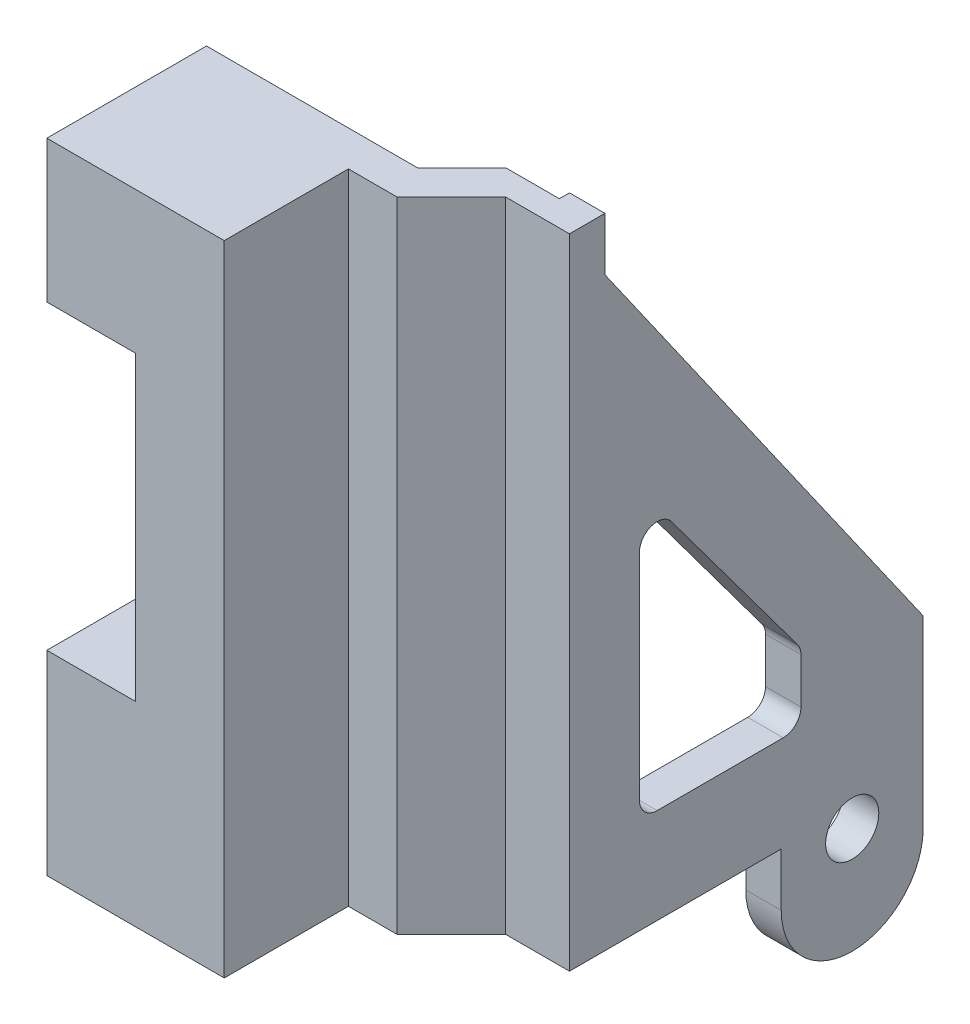
SolidWorks part; units mm, degrees
ref_plane "Front Plane" through (0, 0, 0) normal (0, 0, 1) x (1, 0, 0)
ref_plane "Top Plane" through (0, 0, 0) normal (0, 1, 0) x (1, 0, 0)
ref_plane "Right Plane" through (0, 0, 0) normal (1, 0, 0) x (0, 0, -1)
sketch "Sketch1" plane through (0, 0, 0) normal (0, 1, 0) x (1, 0, 0)
  line L0 (0, 0) -> (11.9097, 0)
  line L1 (11.9097, 0) -> (14.3993, 2.4897)
  line L2 (14.3993, 2.4897) -> (17.3993, 2.4897)
  line L3 (17.3993, 2.4897) -> (17.3993, 21)
  line L4 (0, 0) -> (0, -9)
  line L5 (0, -9) -> (10, -9)
  line L6 (10, -9) -> (10, -2)
  line L7 (10, -2) -> (12.7381, -2)
  line L8 (12.7381, -2) -> (15.7993, 1.0612)
  line L9 (15.7993, 1.0612) -> (19.3993, 1.0612)
  line L10 (19.3993, 1.0612) -> (19.3993, 21)
  line L11 (19.3993, 21) -> (17.3993, 21)
  dimension "D1" = 10
  dimension "D2" = 2.7381
  dimension "D3" = 4.3292
  dimension "D4" = 3
  dimension "D5" = 3.6
  dimension "D6" = 2
  dimension "D7" = 2
  dimension "D8" = 2
  dimension "D9" = 9
  dimension "D10" = 30
  dimension "D11" = 135
extrude "Boss-Extrude1" add sketch "Sketch1" along normal blind 36
sketch "Sketch2" plane through (19.3993, 0, 0) normal (1, 0, 0) x (0, 0, -1)
  line L0 (3.0612, 36) -> (3.0612, 33)
  line L1 (1.0612, 36) -> (21, 36) construction
  line L2 (3.0612, 33) -> (21, 7.3808)
  line L3 (21, 36) -> (21, 0) construction
  line L4 (21, 36) -> (21, 7.3808)
  line L5 (3.0612, 36) -> (21, 36)
  line L6 (1.0612, 36) -> (1.0612, 0) construction
  dimension "D1" = 2
  dimension "D2" = 145
  dimension "D3" = 3
extrude "Cut-Extrude1" cut sketch "Sketch2" against normal up to next
sketch "Sketch3" plane through (19.3993, 0, 0) normal (1, 0, 0) x (0, 0, -1)
  line L0 (6.8092, 19.0751) -> (13.9147, 9.5205)
  line L1 (14.1122, 8.9237) -> (14.1122, 6.3706)
  line L2 (13.1122, 5.3706) -> (6.0068, 5.3706)
  line L3 (5.0068, 6.3706) -> (5.0068, 18.4784)
  line L4 (3.0612, 33) -> (21, 7.3808) construction
  line L5 (1.0612, 36) -> (1.0612, 0) construction
  arc A0 (6.0068, 5.3706) -> (5.0068, 6.3706) centre (6.0068, 6.3706) cw
  arc A1 (6.8092, 19.0751) -> (5.0068, 18.4784) centre (6.0068, 18.4784) ccw
  arc A2 (13.9147, 9.5205) -> (14.1122, 8.9237) centre (13.1122, 8.9237) cw
  arc A3 (14.1122, 6.3706) -> (13.1122, 5.3706) centre (13.1122, 6.3706) cw
extrude "Cut-Extrude2" cut sketch "Sketch3" against normal up to next
sketch "Sketch4" plane through (19.3993, 0, 0) normal (1, 0, 0) x (0, 0, -1)
  line L0 (21, 0) -> (21, -3)
  line L1 (13, 0) -> (13, -3)
  line L6 (21, 0) -> (21, 7.3808)
  line L7 (21, 7.3808) -> (3.0612, 33)
  line L8 (3.0612, 33) -> (3.0612, 36)
  line L9 (3.0612, 36) -> (1.0612, 36)
  line L10 (1.0612, 36) -> (1.0612, 0)
  line L11 (1.0612, 0) -> (21, 0)
  line L17 (13, 0) -> (21, 0)
  arc A0 (21, -3) -> (13, -3) centre (17, -3) cw
  dimension "D3" = 4
  dimension "D2" = 3
  dimension "D1" = 0
extrude "Boss-Extrude2" add sketch "Sketch4" against normal blind 2
sketch "Sketch5" plane through (0, 0, 0) normal (0, 0, -1) x (-1, 0, 0)
  line L0 (0, 11) -> (-5, 11)
  line L1 (0, 36) -> (0, 0) construction
  line L2 (-5, 11) -> (-5, 28)
  line L3 (-5, 28) -> (0, 28)
  line L4 (0, 28) -> (0, 11)
  line L5 (-11.9097, 0) -> (0, 0) construction
  dimension "D1" = 11
  dimension "D2" = 17
  dimension "D3" = 5
extrude "Cut-Extrude3" cut sketch "Sketch5" against normal up to next
sketch "Sketch6" plane through (19.3993, 0, 0) normal (1, 0, 0) x (0, 0, -1)
  line L0 (1.0612, 0) -> (13, 0) construction
  line L1 (13, 0) -> (13, -3) construction
  circle A0 centre (17, -1) radius 1.5
  point P4 (0, 0)
  dimension "D1" = 3
  dimension "D2" = 1
  dimension "D3" = 4
extrude "Cut-Extrude4" cut sketch "Sketch6" against normal up to next
